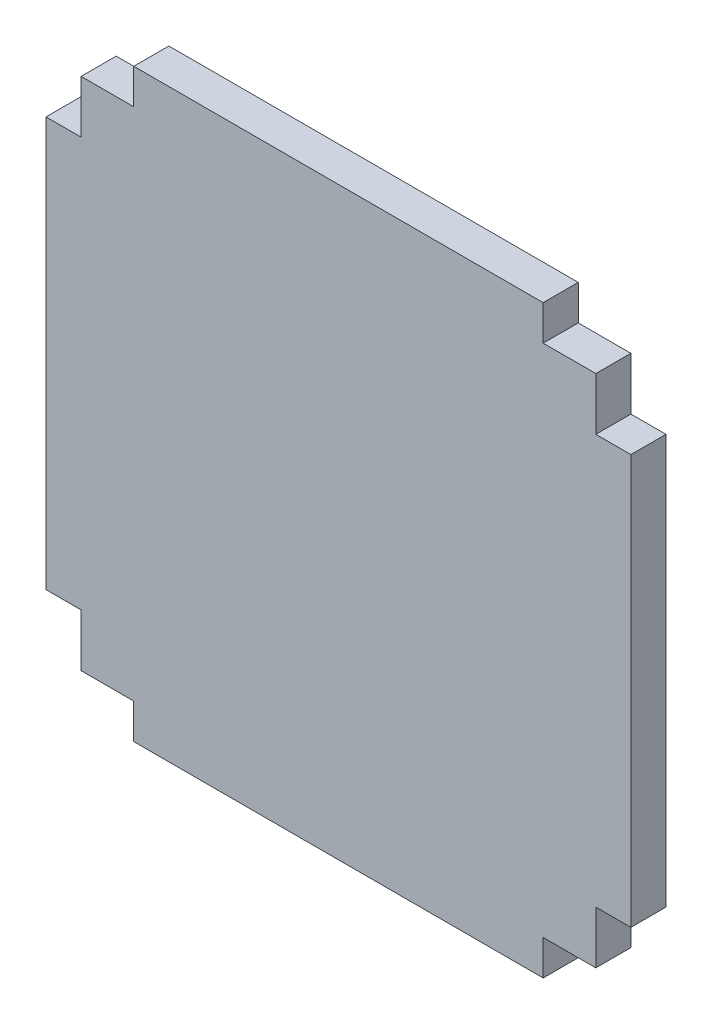
SolidWorks part; units mm, degrees
ref_plane "Piano frontale" through (0, 0, 0) normal (0, 0, 1) x (1, 0, 0)
ref_plane "Piano superiore" through (0, 0, 0) normal (0, 1, 0) x (1, 0, 0)
ref_plane "Piano destro" through (0, 0, 0) normal (1, 0, 0) x (0, 0, -1)
sketch "Schizzo1" plane through (0, 0, 0) normal (0, 0, 1) x (1, 0, 0)
  line L0 (-22, -22) -> (-22, -17.5)
  line L1 (-22, 22) -> (22, 22)
  line L2 (-22, 22) -> (-22, -22)
  line L3 (-22, -22) -> (22, -22)
  line L4 (22, 22) -> (22, -22)
  line L5 (-22, 22) -> (22, -22) construction
  line L6 (-22, -22) -> (22, 22) construction
  line L7 (-22, 22) -> (-22, 17.5)
  line L8 (-22, 22) -> (-17.5, 22)
  line L9 (22, 22) -> (17.5, 22)
  line L10 (22, 22) -> (22, 17.5)
  line L11 (22, -22) -> (22, -17.5)
  line L12 (22, -22) -> (17.5, -22)
  line L13 (-22, -22) -> (-17.5, -22)
  line L14 (-22, 17.5) -> (-25, 17.5)
  line L15 (-25, 17.5) -> (-25, -17.5)
  line L16 (-25, -17.5) -> (-22, -17.5)
  line L17 (-17.5, 22) -> (-17.5, 25)
  line L18 (-17.5, 25) -> (17.5, 25)
  line L19 (17.5, 25) -> (17.5, 22)
  line L20 (22, 17.5) -> (25, 17.5)
  line L21 (25, 17.5) -> (25, -17.5)
  line L22 (25, -17.5) -> (22, -17.5)
  line L23 (17.5, -22) -> (17.5, -25)
  line L24 (17.5, -25) -> (-17.5, -25)
  line L25 (-17.5, -25) -> (-17.5, -22)
  point P0 (0, 0)
  dimension "D1" = 44
  dimension "D2" = 4.5
  dimension "D3" = 4.5
  dimension "D4" = 4.5
  dimension "D5" = 4.5
  dimension "D6" = 4.5
  dimension "D7" = 4.5
  dimension "D8" = 4.5
  dimension "D9" = 4.5
  dimension "D10" = 3
extrude "Estrusione-Estrusione2" add sketch "Schizzo1" along normal blind 3 contours L4 L1 L2 L0 L3 | L25 L24 L23 L3 | L22 L21 L20 L4 | L15 L16 L2 L14 | L19 L18 L17 L1
